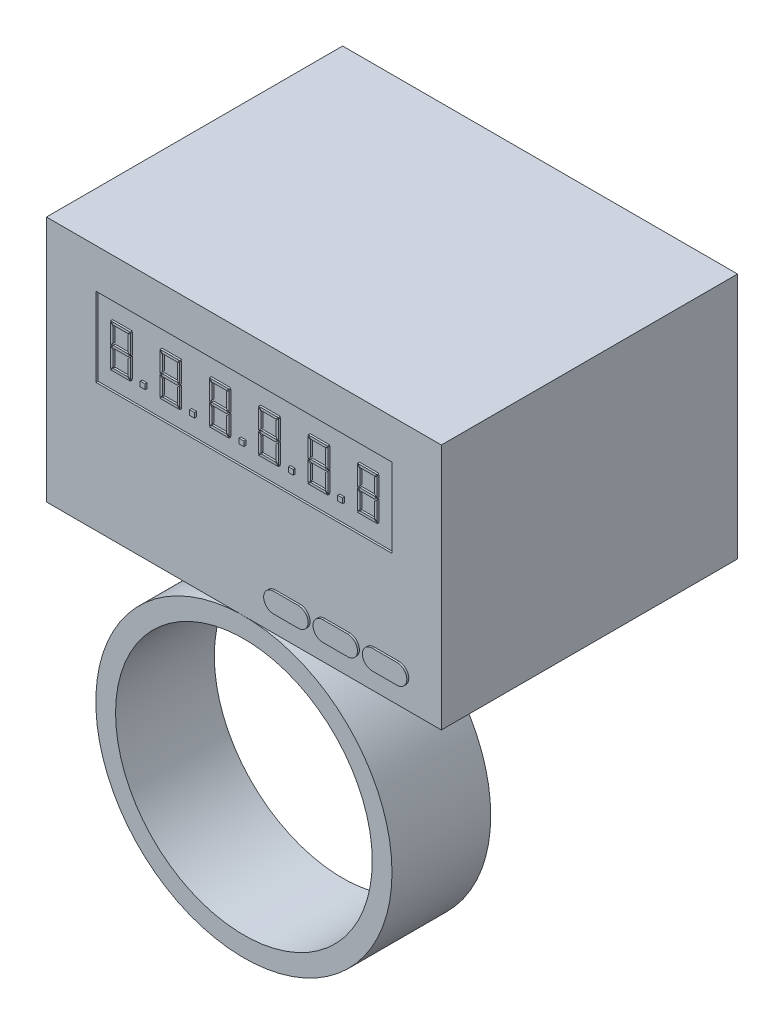
SolidWorks part; units mm, degrees
ref_plane "前视基准面" through (0, 0, 0) normal (0, 0, 1) x (1, 0, 0)
ref_plane "上视基准面" through (0, 0, 0) normal (0, 1, 0) x (1, 0, 0)
ref_plane "右视基准面" through (0, 0, 0) normal (1, 0, 0) x (0, 0, -1)
sketch "草图1" plane through (0, 0, 0) normal (0, 0, 1) x (1, 0, 0)
  line L1 (-30, 15) -> (10, 15)
  line L2 (-30, 15) -> (-30, -10)
  line L3 (-30, -10) -> (10, -10)
  line L4 (10, 15) -> (10, -10)
  dimension "D1" = 40
  dimension "D2" = 25
  dimension "D3" = 30
  dimension "D4" = 15
extrude "凸台-拉伸1" add sketch "草图1" against normal blind 30
sketch "草图2" plane through (0, 0, 0) normal (0, 0, 1) x (1, 0, 0)
  line L0 (10, 15) -> (-30, 15) construction
  line L1 (-25, 11) -> (5, 11)
  line L2 (-25, 11) -> (-25, 3)
  line L3 (-25, 3) -> (5, 3)
  line L4 (5, 11) -> (5, 3)
  line L5 (-30, 15) -> (-30, -10) construction
  dimension "D1" = 30
  dimension "D2" = 8
  dimension "D3" = 4
  dimension "D4" = 5
extrude "切除-拉伸1" cut sketch "草图2" against normal blind 0.2
sketch "草图3" plane through (0, 0, -0.2) normal (0, 0, 1) x (1, 0, 0)
  line L0 (-25, 11) -> (-25, 3) construction
  line L1 (-23.5, 9.05) -> (-23.25, 8.8)
  line L2 (-23.5, 9.05) -> (-23.5, 7.05)
  line L3 (-23.5, 7.05) -> (-23.25, 7.3)
  line L4 (-25, 11) -> (-25, 3) construction
  line L5 (-23.5, 9.15) -> (-21.5, 9.15)
  line L6 (-23.25, 8.8) -> (-23.25, 7.3)
  line L7 (-23.25, 8.9) -> (-21.75, 8.9)
  line L9 (-21.75, 7.125) -> (-23.25, 7.125)
  line L10 (-21.75, 6.875) -> (-23.25, 6.875)
  line L11 (-21.75, 7.125) -> (-21.625, 7.0021)
  line L12 (-21.75, 6.875) -> (-21.625, 7.0021)
  line L13 (-23.25, 6.875) -> (-23.375, 7.0021)
  line L14 (-23.5, 9.15) -> (-23.25, 8.9)
  line L15 (-21.5, 9.15) -> (-21.75, 8.9)
  line L16 (-22.5, 9.15) -> (-22.5, 5.5864) construction
  line L17 (-18.0349, 7) -> (-13.1621, 7) construction
  line L18 (-21.5, 4.85) -> (-21.75, 5.1)
  line L19 (-23.5, 4.85) -> (-23.25, 5.1)
  line L20 (-23.25, 5.1) -> (-21.75, 5.1)
  line L21 (-23.25, 5.2) -> (-23.25, 6.7)
  line L22 (-23.5, 4.85) -> (-21.5, 4.85)
  line L24 (-23.5, 6.95) -> (-23.25, 6.7)
  line L25 (-23.5, 4.95) -> (-23.5, 6.95)
  line L26 (-23.5, 4.95) -> (-23.25, 5.2)
  line L27 (-21.5, 4.95) -> (-21.75, 5.2)
  line L28 (-21.5, 4.95) -> (-21.5, 6.95)
  line L29 (-21.5, 6.95) -> (-21.75, 6.7)
  line L30 (-21.75, 5.2) -> (-21.75, 6.7)
  line L31 (-21.75, 8.8) -> (-21.75, 7.3)
  line L32 (-21.5, 7.05) -> (-21.75, 7.3)
  line L33 (-21.5, 9.05) -> (-21.5, 7.05)
  line L34 (-21.5, 9.05) -> (-21.75, 8.8)
  line L35 (-23.25, 7.125) -> (-23.375, 7.0021)
  line L36 (5, 11) -> (-25, 11) construction
  dimension "D1" = 2
  dimension "D2" = 0.1
  dimension "D3" = 4
  dimension "D4" = 2
  dimension "D5" = 0.125
  dimension "D6" = 0.125
  dimension "D7" = 1.5
  dimension "D8" = 0.25
  dimension "D9" = 0.05
  dimension "D10" = 0.25
  dimension "D11" = 2.5
  dimension "D12" = 0.25
  dimension "D13" = 0.25
  dimension "D14" = 0.25
  dimension "D15" = 0.25
  dimension "D16" = 0.125
  dimension "D17" = 0.125
  dimension "D18" = 1.5
extrude "凸台-拉伸2" add sketch "草图3" along normal blind 0.2
sketch "草图4" plane through (0, 0, -0.2) normal (0, 0, 1) x (1, 0, 0)
  line L1 (-21.5, 4.95) -> (-21.5, 6.95) construction
  line L2 (-20.5, 4.85) -> (-20, 4.85)
  line L3 (-20.5, 4.85) -> (-20.5, 5.35)
  line L4 (-20.5, 5.35) -> (-20, 5.35)
  line L5 (-20, 4.85) -> (-20, 5.35)
  line L6 (-23.5, 4.85) -> (-21.5, 4.85) construction
  dimension "D1" = 0.5
  dimension "D2" = 0.5
  dimension "D3" = 1
extrude "凸台-拉伸3" add sketch "草图4" along normal blind 0.2
pattern_linear "阵列(线性)3" count 6 spacing 5 along (1, 0, 0) of "凸台-拉伸2"
pattern_linear "阵列(线性)4" count 5 spacing 5 along (1, 0, 0) of "凸台-拉伸3"
sketch "草图5" plane through (0, 0, 0) normal (0, 0, 1) x (1, 0, 0)
  line L0 (-6.7997, -7.1218) -> (-4.2997, -7.1218) construction
  line L1 (-6.7997, -6.1218) -> (-4.2997, -6.1218)
  line L2 (-6.7997, -8.1218) -> (-4.2997, -8.1218)
  arc A0 (-6.7997, -6.1218) -> (-6.7997, -8.1218) centre (-6.7997, -7.1218) ccw
  arc A1 (-4.2997, -8.1218) -> (-4.2997, -6.1218) centre (-4.2997, -7.1218) ccw
  point P2 (-5.5497, -7.1218)
  dimension "D6" = 1
  dimension "D5" = 2.5
extrude "凸台-拉伸4" add sketch "草图5" along normal blind 0.2
pattern_linear "阵列(线性)5" count 3 spacing 5 along (1, 0, 0) of "凸台-拉伸4"
sketch "草图6" plane through (0, 0, 0) normal (0, 0, 1) x (1, 0, 0)
  line L0 (-30, -10) -> (10, -10) construction
  circle A0 centre (-10, -25) radius 15
  circle A1 centre (-10, -25) radius 13
  dimension "D1" = 30
  dimension "D3" = 26
  dimension "D2" = 10
extrude "凸台-拉伸5" add sketch "草图6" against normal blind 10 separate body
